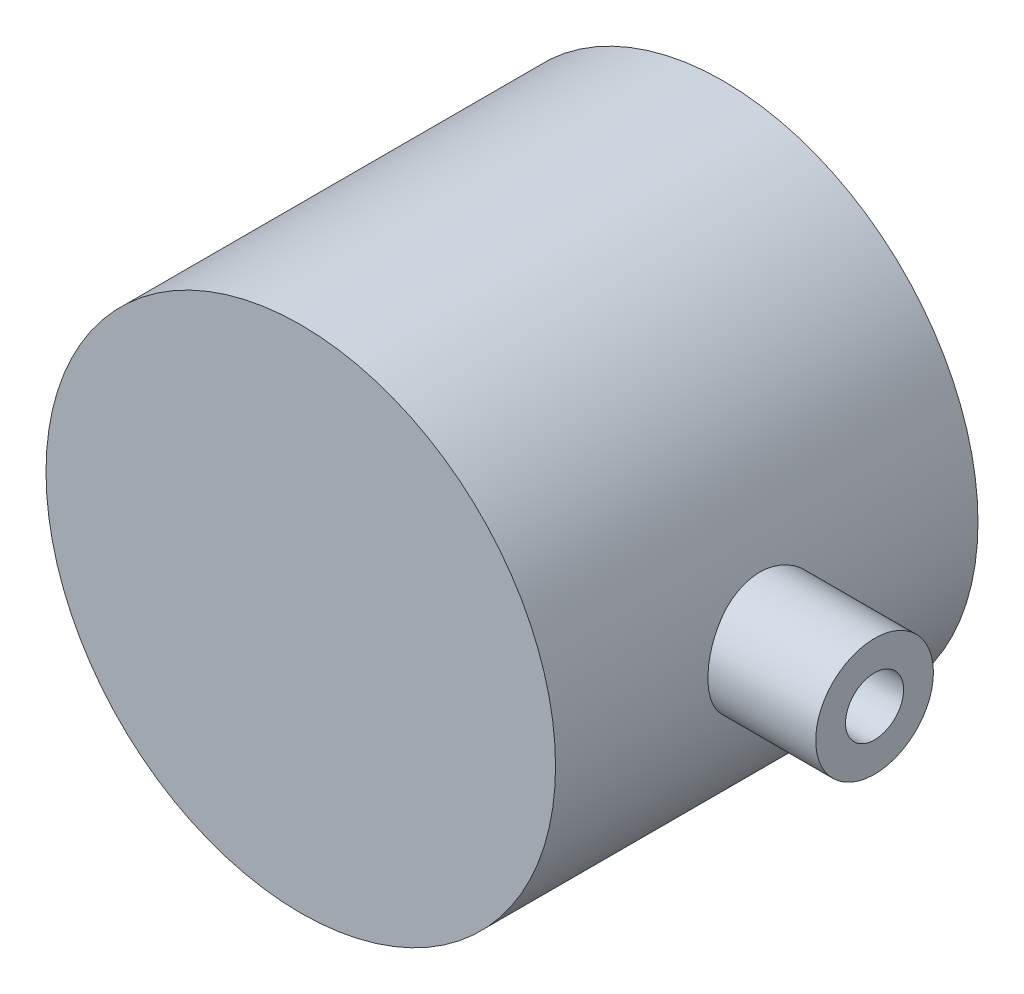
SolidWorks part; units mm, degrees
ref_plane "Ebene vorne" through (0, 0, 0) normal (0, 0, 1) x (1, 0, 0)
ref_plane "Ebene oben" through (0, 0, 0) normal (0, 1, 0) x (1, 0, 0)
ref_plane "Ebene rechts" through (0, 0, 0) normal (1, 0, 0) x (0, 0, -1)
sketch "Sketch1" plane through (0, 0, 0) normal (0, 0, 1) x (1, 0, 0)
  circle A1 centre (0, 0) radius 24.123
  dimension "D3" = 48.246
extrude "Boss-Extrude1" add sketch "Sketch1" along normal blind 35 and the other way blind 5
sketch "Sketch2" plane through (0, 0, 0) normal (1, 0, 0) x (0, 0, -1)
  line L0 (0, 24.123) -> (0, -24.123) construction
  circle A0 centre (-15, 0) radius 3.25
  dimension "D1" = 15
  dimension "D2" = 6.5
extrude "Cut-Extrude2" cut sketch "Sketch2" against normal blind 19.09 and the other way blind 19.25
sketch "Sketch4" plane through (0, 0, 0) normal (0, 1, 0) x (1, 0, 0)
  line L0 (0, -18.25) -> (0, -11.75) construction
  line L1 (-24.123, 0) -> (24.123, 0) construction
  circle A0 centre (0, -15) radius 3.25
  dimension "D1" = 15
  dimension "D2" = 6.5
extrude "Cut-Extrude3" cut sketch "Sketch4" against normal blind 19.09
sketch "Sketch5" plane through (0, 0, 0) normal (1, 0, 0) x (0, 0, -1)
  circle A0 centre (-15, 0) radius 5.25
  dimension "D1" = 10.5
extrude "Cut-Extrude8" cut sketch "Sketch5" along normal blind 4.533 from offset 24.123 contours A0 offset against normal yes
sketch "Sketch6" plane through (0, 0, 0) normal (0, 1, 0) x (1, 0, 0)
  line L0 (0, -18.25) -> (0, -11.75) construction
  line L1 (-24.123, -35) -> (24.123, -35) construction
  circle A0 centre (0, -15) radius 5.25
  dimension "D1" = 20
  dimension "D2" = 10.5
extrude "Cut-Extrude9" cut sketch "Sketch6" along normal blind 4.533 from offset 24.123 offset against normal yes
sketch "Sketch7" plane through (0, 0, -5) normal (0, 0, -1) x (-1, 0, 0)
  circle A0 centre (0, 0) radius 17.25
  dimension "D1" = 34.5
extrude "Cut-Extrude10" cut sketch "Sketch7" against normal blind 30
sketch "Sketch8" plane through (0, 0, 0) normal (1, 0, 0) x (0, 0, -1)
  circle A0 centre (-15, 0) radius 2.75
  dimension "D1" = 5.5
extrude "Cut-Extrude11" cut sketch "Sketch8" along normal blind 24.873 and the other way blind 50 from offset 19.25
sketch "Sketch9" plane through (0, 0, 0) normal (1, 0, 0) x (0, 0, -1)
  circle A0 centre (-15, 0) radius 5.575
extrude "Boss-Extrude2" add sketch "Sketch9" along normal blind 11.203 from offset 23.125 separate body
extrude "Cut-Extrude12" cut sketch "Sketch8" along normal blind 50
sketch "Sketch11" plane through (0, 0, 0) normal (1, 0, 0) x (0, 0, -1)
  circle A0 centre (-15, 0) radius 8.25
  dimension "D1" = 16.5
extrude "Cut-Extrude13" cut sketch "Sketch11" along normal blind 2 from offset 24.125 offset against normal yes
sketch "Sketch12" plane through (0, 0, 0) normal (0, 1, 0) x (1, 0, 0)
  circle A0 centre (0, -15) radius 8.25
  dimension "D1" = 16.5
extrude "Cut-Extrude14" cut sketch "Sketch12" along normal blind 2 from offset 24.125 offset against normal yes
sketch "Sketch13" plane through (0, 0, 0) normal (0, 1, 0) x (1, 0, 0)
  circle A0 centre (0, -15) radius 2.75
  dimension "D1" = 5.5
extrude "Cut-Extrude15" cut sketch "Sketch13" against normal blind 30
